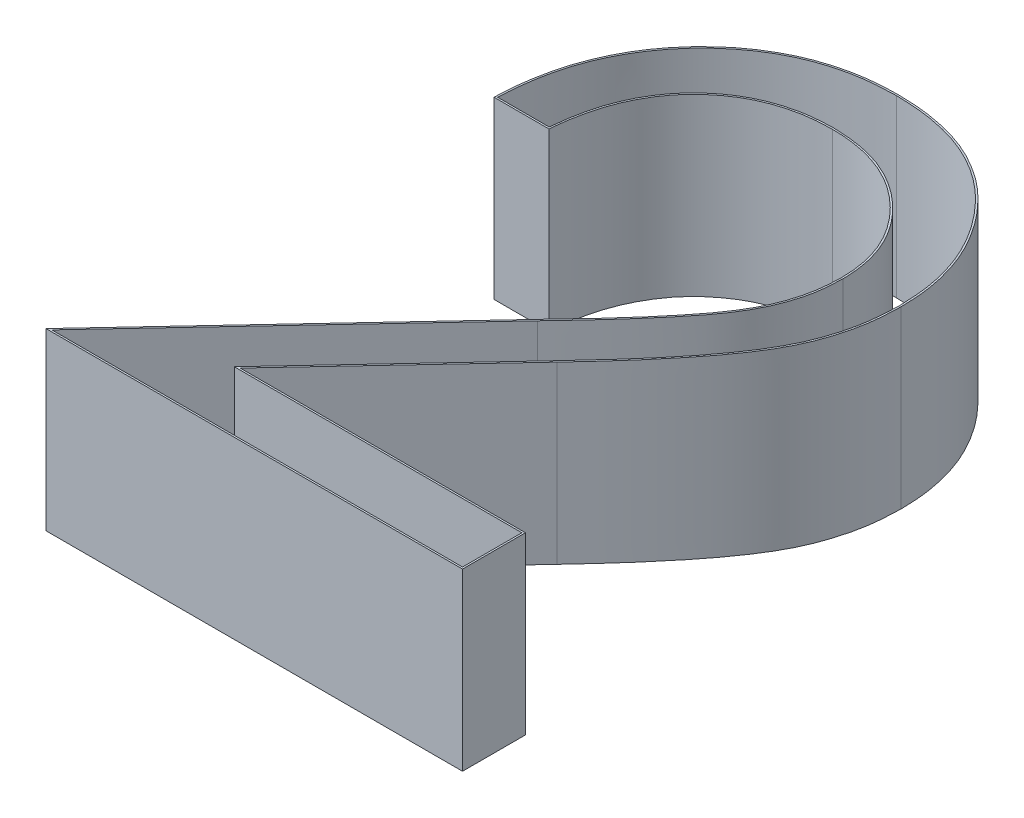
SolidWorks part; units mm, degrees
ref_plane "Front Plane" through (0, 0, 0) normal (0, 0, 1) x (1, 0, 0)
ref_plane "Top Plane" through (0, 0, 0) normal (0, 1, 0) x (1, 0, 0)
ref_plane "Right Plane" through (0, 0, 0) normal (1, 0, 0) x (0, 0, -1)
sketch "Sketch1" plane through (0, 0, 0) normal (0, 1, 0) x (1, 0, 0)
  text T0 "2"
  point P0 (0, 0)
extrude "Boss-Extrude1" add sketch "Sketch1" along normal blind 1
sketch "Sketch2" plane through (0, 1, 0) normal (0, 1, 0) x (1, 0, 0)
  line L18 (1.4992, 1.4416) -> (0.1577, 0.01)
  line L19 (0.1577, 0.01) -> (2.5028, 0.01)
  line L20 (2.5028, 0.01) -> (2.5028, 0.349)
  line L21 (2.5028, 0.349) -> (0.861, 0.349)
  line L22 (0.861, 0.349) -> (1.7525, 1.3004)
  line L23 (0.2797, 2.4331) -> (0.5742, 2.4331)
  line L24 (1.4992, 1.4416) -> (0.1577, 0.01)
  line L25 (0.1577, 0.01) -> (2.5028, 0.01)
  line L26 (2.5028, 0.01) -> (2.5028, 0.349)
  line L27 (2.5028, 0.349) -> (0.861, 0.349)
  line L28 (0.861, 0.349) -> (1.7525, 1.3004)
  line L29 (0.2797, 2.4331) -> (0.5742, 2.4331)
  spline S18 degree 3 poles (-3862.5508, 1039.313) (99.054, -40.2215) (-2.1695, -4.4606) (0.6803, 2.8398) (0.7375, 2.9332) (0.8883, 3.0853) (0.9782, 3.1463) (1.1292, 3.2042) (1.1808, 3.2184) (6.0587, 4.0642) (23.3766, -49.0958) (-1251.3873, 3801.7648) knots -18.044241 -18.044241 -18.044241 -18.044241 0.25 0.25 0.5 0.5 0.75 0.75 0.875 0.875 12.311304 12.311304 12.311304 12.311304 only from (0.5742, 2.4331) to (1.3945, 3.2408)
  spline S19 degree 3 poles (765.81, 3929.3467) (-30.328, -98.5984) (-4.7089, 5.5675) (1.7741, 3.1573) (1.856, 3.1056) (2.0017, 2.973) (2.0622, 2.8947) (2.124, 2.7617) (2.1387, 2.7153) (3.1425, -2.042) (-58.3203, -20.3107) (3733.7769, 1442.5863) knots -17.022207 -17.022207 -17.022207 -17.022207 0.25 0.25 0.5 0.5 0.75 0.75 0.875 0.875 13.171454 13.171454 13.171454 13.171454 only from (1.3945, 3.2408) to (2.1639, 2.5212)
  spline S20 degree 3 poles (3912.2631, -839.9217) (-50.0328, 23.0848) (3.0329, 6.8151) (2.1379, 2.3065) (2.1218, 2.2549) (2.0592, 2.1033) (1.9985, 2.0123) (-6.93, -9.3033) (-78.3091, 25.0703) (3366.1311, -2161.2662) knots -10.424094 -10.424094 -10.424094 -10.424094 0.125 0.125 0.25 0.25 0.5 0.5 33.582483 33.582483 33.582483 33.582483 only from (2.1639, 2.5212) to (1.4992, 1.4416)
  spline S21 degree 3 poles (3193.5322, -2409.1647) (-80.727, 35.328) (-4.811, -8.3026) (2.2977, 1.9646) (2.3589, 2.0705) (2.4183, 2.2457) (2.4336, 2.3056) (3.2699, 7.451) (-47.5184, 20.3977) (3958.8845, -584.6098) knots -24.624281 -24.624281 -24.624281 -24.624281 0.5 0.5 0.75 0.75 0.875 0.875 11.405311 11.405311 11.405311 11.405311 only from (1.7525, 1.3004) to (2.4579, 2.5493)
  spline S22 degree 3 poles (3948.6701, 655.8488) (-56.8095, -18.689) (3.4908, -2.7583) (2.4266, 2.8203) (2.4075, 2.887) (2.3283, 3.0769) (2.2492, 3.1904) (2.0581, 3.3861) (1.9407, 3.4637) (1.75, 3.5355) (1.6837, 3.5521) (-4.2941, 4.5522) (-15.2926, -55.3372) (316.9137, 3990.8078) knots -10.171649 -10.171649 -10.171649 -10.171649 0.125 0.125 0.25 0.25 0.5 0.5 0.75 0.75 0.875 0.875 11.757444 11.757444 11.757444 11.757444 only from (2.4579, 2.5493) to (1.4107, 3.5797)
  spline S23 degree 3 poles (-625.751, 3953.9377) (23.9542, -60.0047) (7.194, 4.6843) (1.115, 3.5468) (1.0421, 3.5262) (0.8348, 3.4407) (0.7111, 3.3538) (0.5032, 3.1393) (0.4202, 3.0108) (0.3384, 2.8033) (0.3183, 2.7309) (-1.0334, -4.3151) (66.2887, -19.5619) (-3973.2437, 460.1447) knots -10.154878 -10.154878 -10.154878 -10.154878 0.125 0.125 0.25 0.25 0.5 0.5 0.75 0.75 0.875 0.875 12.66706 12.66706 12.66706 12.66706 only from (1.4107, 3.5797) to (0.2797, 2.4331)
  spline S24 degree 3 poles (0.5742, 2.4331) (0.5844, 2.5392) (0.6034, 2.643) (0.6803, 2.8398) (0.7375, 2.9332) (0.8883, 3.0853) (0.9782, 3.1463) (1.1292, 3.2042) (1.1808, 3.2184) (1.2863, 3.2367) (1.3405, 3.2394) (1.3945, 3.2408) knots 0 0 0 0 0.25 0.25 0.5 0.5 0.75 0.75 0.875 0.875 1 1 1 1
  spline S25 degree 3 poles (1.3945, 3.2408) (1.4925, 3.2382) (1.5891, 3.2261) (1.7741, 3.1573) (1.856, 3.1056) (2.0017, 2.973) (2.0622, 2.8947) (2.124, 2.7617) (2.1387, 2.7153) (2.1589, 2.6196) (2.1625, 2.5703) (2.1639, 2.5212) knots 0 0 0 0 0.25 0.25 0.5 0.5 0.75 0.75 0.875 0.875 1 1 1 1
  spline S26 degree 3 poles (2.1639, 2.5212) (2.1617, 2.4665) (2.1588, 2.4121) (2.1379, 2.3065) (2.1218, 2.2549) (2.0592, 2.1033) (1.9985, 2.0123) (1.7976, 1.7577) (1.6494, 1.5984) (1.4992, 1.4416) knots 0 0 0 0 0.125 0.125 0.25 0.25 0.5 0.5 1 1 1 1
  spline S27 degree 3 poles (1.7525, 1.3004) (1.9202, 1.4801) (2.0876, 1.6611) (2.2977, 1.9646) (2.3589, 2.0705) (2.4183, 2.2457) (2.4336, 2.3056) (2.4533, 2.4263) (2.4558, 2.4878) (2.4579, 2.5493) knots 0 0 0 0 0.5 0.5 0.75 0.75 0.875 0.875 1 1 1 1
  spline S28 degree 3 poles (2.4579, 2.5493) (2.4559, 2.618) (2.4522, 2.6865) (2.4266, 2.8203) (2.4075, 2.887) (2.3283, 3.0769) (2.2492, 3.1904) (2.0581, 3.3861) (1.9407, 3.4637) (1.75, 3.5355) (1.6837, 3.5521) (1.5479, 3.5748) (1.4793, 3.5781) (1.4107, 3.5797) knots 0 0 0 0 0.125 0.125 0.25 0.25 0.5 0.5 0.75 0.75 0.875 0.875 1 1 1 1
  spline S29 degree 3 poles (1.4107, 3.5797) (1.3357, 3.5781) (1.261, 3.5742) (1.115, 3.5468) (1.0421, 3.5262) (0.8348, 3.4407) (0.7111, 3.3538) (0.5032, 3.1393) (0.4202, 3.0108) (0.3384, 2.8033) (0.3183, 2.7309) (0.2899, 2.5831) (0.2835, 2.5082) (0.2797, 2.4331) knots 0 0 0 0 0.125 0.125 0.25 0.25 0.5 0.5 0.75 0.75 0.875 0.875 1 1 1 1
  dimension "D1" = 0.01
extrude "Cut-Extrude1" cut sketch "Sketch2" against normal blind 1
